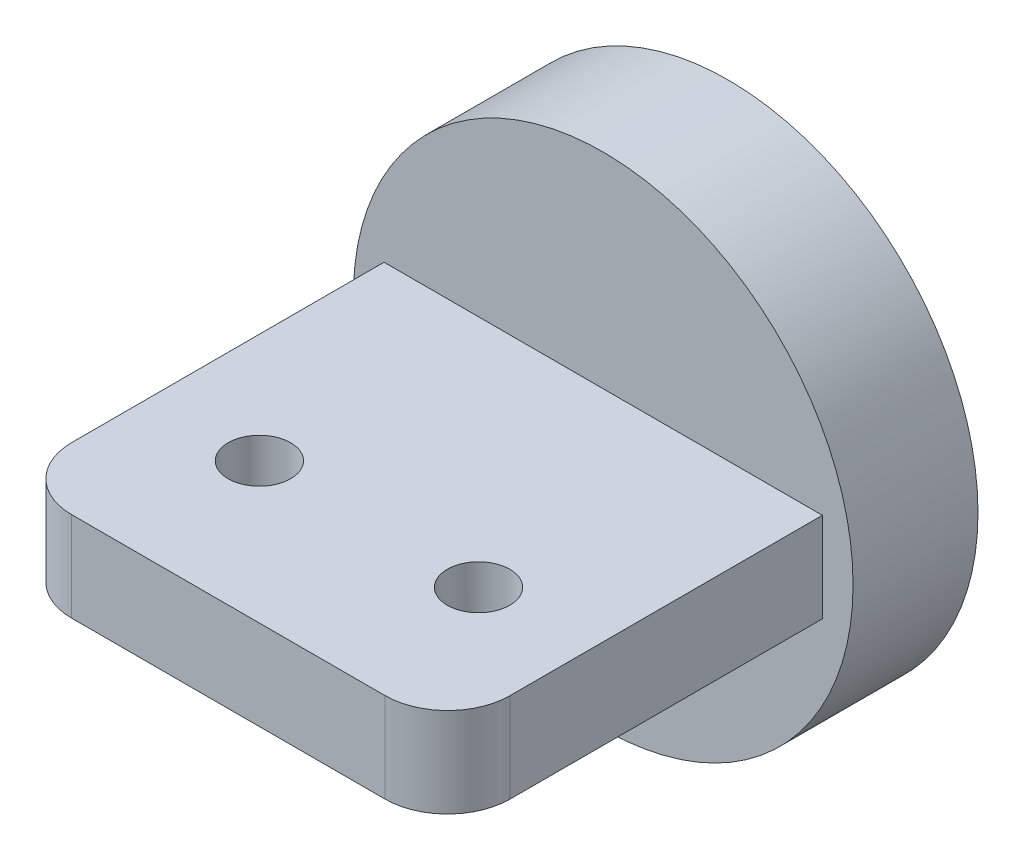
SolidWorks part; units mm, degrees
material "Gray Cast Iron"
ref_plane "Front Plane" through (0, 0, 0) normal (0, 0, 1) x (1, 0, 0)
ref_plane "Top Plane" through (0, 0, 0) normal (0, 1, 0) x (1, 0, 0)
ref_plane "Right Plane" through (0, 0, 0) normal (1, 0, 0) x (0, 0, -1)
sketch "Sketch1" plane through (0, 0, 0) normal (0, 0, 1) x (1, 0, 0)
  circle A0 centre (0, 0) radius 20
  dimension "D1" = 40
extrude "Boss-Extrude1" add sketch "Sketch1" along normal blind 10
sketch "Sketch2" plane through (0, 0, 10) normal (0, 0, 1) x (1, 0, 0)
  line L1 (-17.5413, 3.588) -> (17.5413, 3.588)
  line L2 (-17.5413, 3.588) -> (-17.5413, -3.588)
  line L3 (-17.5413, -3.588) -> (17.5413, -3.588)
  line L4 (17.5413, 3.588) -> (17.5413, -3.588)
  line L5 (-17.5413, 3.588) -> (17.5413, -3.588) construction
  line L6 (-17.5413, -3.588) -> (17.5413, 3.588) construction
  point P0 (0, 0)
extrude "Boss-Extrude2" add sketch "Sketch2" along normal blind 30
fillet "Fillet1" radius 5 2 edges at (17.5413, 0, 40) (-17.5413, 0, 40)
sketch "Sketch3" plane through (0, 3.588, 0) normal (0, 1, 0) x (1, 0, 0)
  line L0 (0, -40) -> (0, -10) construction
  line L1 (12.5413, -40) -> (-12.5413, -40) construction
  line L2 (17.5413, -10) -> (-17.5413, -10) construction
  line L3 (-17.5413, -35) -> (17.5413, -35) construction
  line L4 (-17.5413, -22.5) -> (17.5413, -22.5) construction
  line L5 (-17.5413, -35) -> (-17.5413, -10) construction
  line L6 (17.5413, -35) -> (17.5413, -10) construction
  line L7 (-17.5413, -22.5) -> (0, -35) construction
  line L8 (0, -35) -> (0, -22.5) construction
  line L9 (0, -22.5) -> (-17.5413, -35) construction
  circle A0 centre (-8.7707, -28.75) radius 2.5
  circle A1 centre (8.7707, -28.75) radius 2.5
  dimension "D1" = 5
extrude "Cut-Extrude1" cut sketch "Sketch3" against normal blind 30
sketch "Sketch4" plane through (0, 0, 0) normal (0, 0, -1) x (-1, 0, 0)
  circle A0 centre (0, 0) radius 10
  dimension "D1" = 20
extrude "Cut-Extrude2" cut sketch "Sketch4" against normal blind 5
